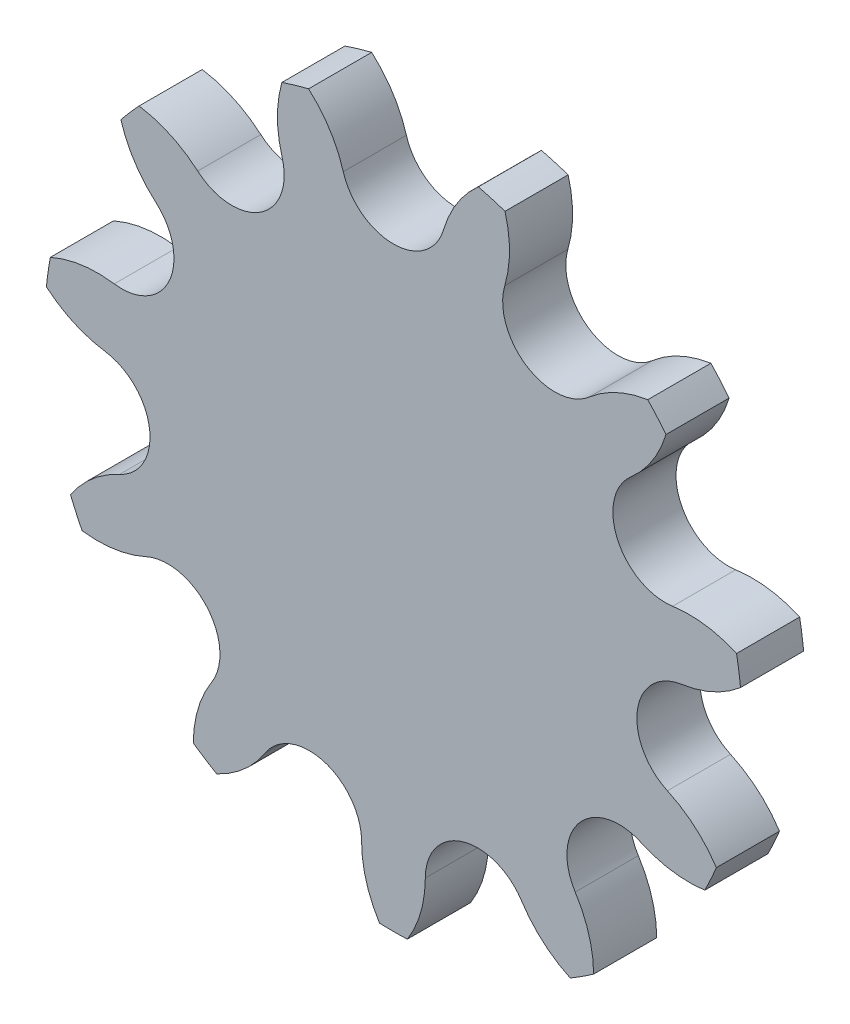
SolidWorks part; units mm, degrees
material "AISI 1020"
ref_plane "Спереди" through (0, 0, 0) normal (0, 0, 1) x (1, 0, 0)
ref_plane "Сверху" through (0, 0, 0) normal (0, 1, 0) x (1, 0, 0)
ref_plane "Справа" through (0, 0, 0) normal (1, 0, 0) x (0, 0, -1)
sketch "Эскиз1" plane through (0, 0, 0) normal (0, 0, 1) x (1, 0, 0)
  line L4 (0, 0) -> (0, 14.1979)
  line L5 (0, 14.1979) -> (7.6759, 11.944)
  line L6 (7.6759, 11.944) -> (0, 0)
  circle A1 centre (0, 14.1979) radius 2.385
  circle A2 centre (7.6759, 11.944) radius 2.385
  circle A3 centre (0, 0) radius 16.5829 construction
  dimension "D6" = 4.77
  dimension "D1" = 33.1657
  dimension "D5" = 32.727
  dimension "D7" = 8
sketch "Эскиз2" plane through (0, 0, 0) normal (0, 0, 1) x (1, 0, 0)
  line L0 (0, 0) -> (0, 11.7129)
  line L1 (0, 0) -> (6.3325, 9.8535)
  line L4 (7.6759, 11.944) -> (0, 0) construction
  arc A0 (5.2916, 12.6441) -> (5.3031, 15.7121) centre (0, 14.1979) ccw
  arc A1 (0, 16.5829) -> (8.9654, 13.9504) centre (0, 0) cw construction
  circle A2 centre (0, 14.1979) radius 2.385 construction
  circle A3 centre (7.6759, 11.944) radius 2.385 construction
  circle A5 centre (0, 14.1979) radius 2.485
  arc A6 (0, 11.7129) -> (2.3843, 13.4978) centre (0, 14.1979) ccw
  arc A7 (4.0334, 16.0849) -> (2.3843, 13.4978) centre (7.6759, 11.944) ccw
  circle A8 centre (7.6759, 11.944) radius 2.485
  arc A9 (5.2916, 12.6441) -> (6.3325, 9.8535) centre (7.6759, 11.944) ccw
  arc A10 (4.0334, 16.0849) -> (5.3031, 15.7121) centre (0, 0) cw
  dimension "D1" = 0.1
  dimension "D2" = 0.1
extrude "Бобышка-Вытянуть1" add sketch "Эскиз2" along normal blind 3
pattern_circular "Круговой массив1" count 11 over 360 about axis through (0, 0, 0) along (0, 0, 1) of "Бобышка-Вытянуть1"
sketch "Эскиз3" plane through (0, 0, 3) normal (0, 0, 1) x (1, 0, 0)
  line L0 (0, 0) -> (0, 30) construction
  line L1 (0, 0) -> (25.9808, 15) construction
  circle A0 centre (0, 0) radius 17.5
  circle A1 centre (0, 0) radius 30 construction
  circle A2 centre (0, 30) radius 4
  circle A3 centre (25.9808, 15) radius 4
  circle A4 centre (25.9808, -15) radius 4
  circle A5 centre (0, -30) radius 4
  circle A6 centre (-25.9808, -15) radius 4
  circle A7 centre (-25.9808, 15) radius 4
  dimension "D1" = 35
  dimension "D2" = 60
  dimension "D3" = 8
  dimension "D5" = 60
  dimension "D6" = 30
  dimension "D4" = 6
extrude "Вырез-Вытянуть1" [suppressed] cut sketch "Эскиз3" against normal through all
equation "\"D5@Эскиз1\"=360/\"_kol-vo\""
equation "\"_kol-vo\" = 11"
equation "\"_Pitch\" = 8"
equation "\"_d1_max\" = 4.77"
equation "\"_d1_min\" = 3.28"
equation "\"_d2_max\" = 3.28"
equation "\"_T_max\"= 1.6"
equation "\"_h2\"= 9.5"
equation "\"_L_max\" = 13.9"
equation "\"_Lc_max\" = 13.9"
equation "\"D6@Эскиз1\"=\"_d1_max\""
equation "\"D1@Круговой массив1\"=\"_kol-vo\""
equation "\"D7@Эскиз1\"=\"_Pitch\""
